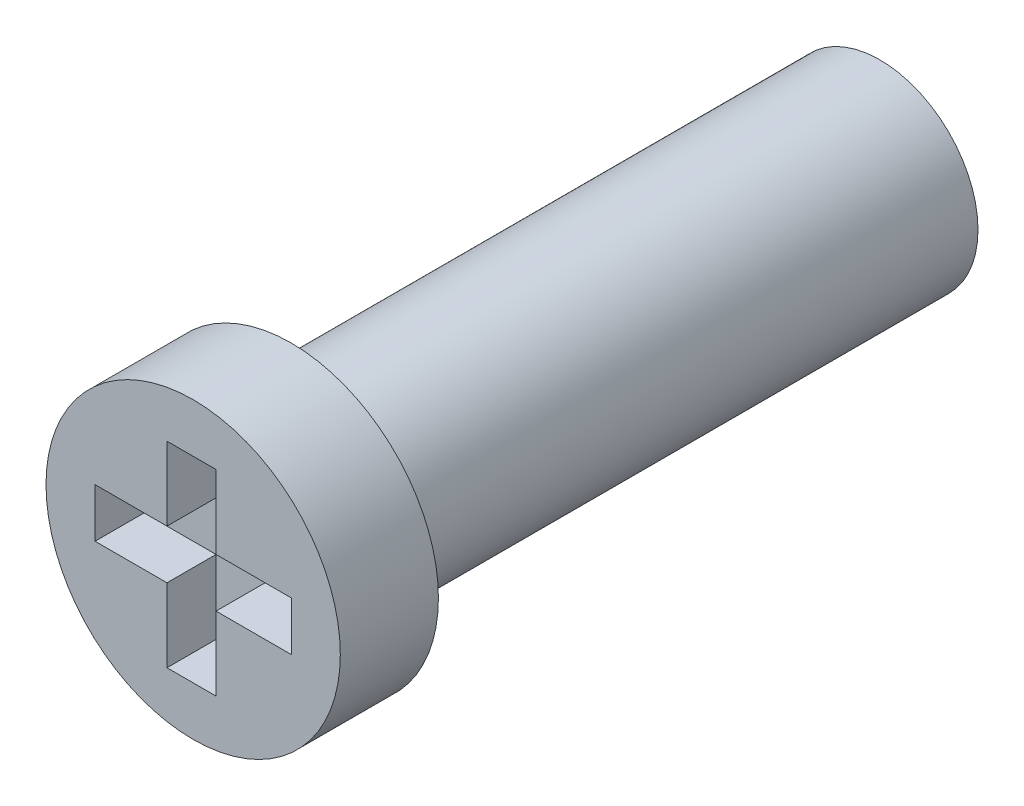
SolidWorks part; units mm, degrees
material "1.4000 (X6Cr13)"
ref_plane "Płaszczyzna XY" through (0, 0, 0) normal (0, 0, 1) x (1, 0, 0)
ref_plane "Płaszczyzna XZ" through (0, 0, 0) normal (0, 1, 0) x (1, 0, 0)
ref_plane "Płaszczyzna YZ" through (0, 0, 0) normal (1, 0, 0) x (0, 0, -1)
sketch "Szkic1" plane through (0, 0, 0) normal (0, 0, 1) x (1, 0, 0)
  circle A0 centre (0, 0) radius 2
extrude "Dodanie-wyciągnięcie1" add sketch "Szkic1" along normal blind 12
sketch "Szkic2" plane through (0, 0, 12) normal (0, 0, 1) x (1, 0, 0)
  circle A0 centre (0, 0) radius 3
extrude "Dodanie-wyciągnięcie2" add sketch "Szkic2" along normal blind 2
sketch "Szkic3" plane through (0, 0, 14) normal (0, 0, 1) x (1, 0, 0)
  line L0 (0.4665, 0.5) -> (2, 0.5)
  line L1 (-0.5335, 2) -> (0.4665, 2)
  line L2 (-0.5335, 2) -> (-0.5335, 0.5)
  line L3 (-0.5335, -2) -> (0.4665, -2)
  line L4 (0.4665, 2) -> (0.4665, 0.5)
  line L5 (-2, -0.5) -> (-0.5335, -0.5)
  line L6 (-2, -0.5) -> (-2, 0.5)
  line L7 (-2, 0.5) -> (-0.5335, 0.5)
  line L8 (2, -0.5) -> (2, 0.5)
  line L9 (0.4665, -0.5) -> (2, -0.5)
  line L12 (0.4665, -0.5) -> (0.4665, -2)
  line L13 (-0.5335, -0.5) -> (-0.5335, -2)
  circle A1 centre (0, 0) radius 3 construction
  point P6 (0, 0)
  dimension "D1" = 1
  dimension "D2" = 4
  dimension "D3" = 2
  dimension "D4" = 1
  dimension "D5" = 4
extrude "Wytnij-wyciągnięcie1" cut sketch "Szkic3" against normal blind 1
